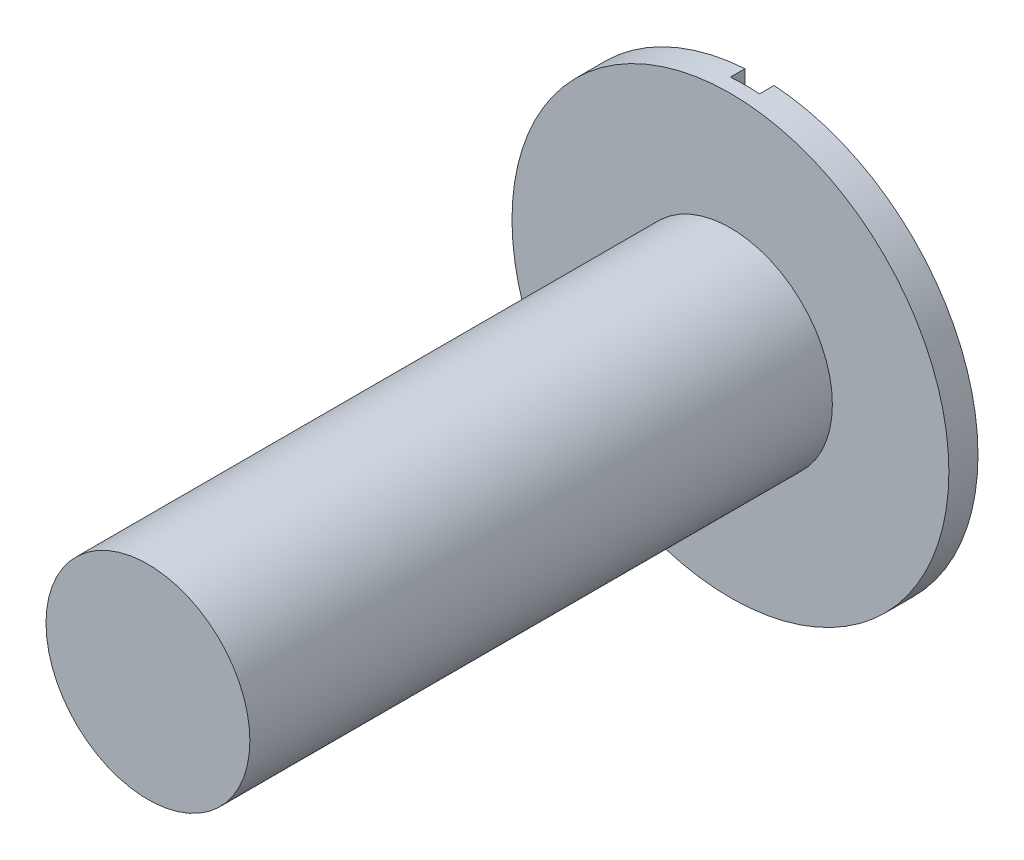
SolidWorks part; units mm, degrees
ref_plane "Alzado" through (0, 0, 0) normal (0, 0, 1) x (1, 0, 0)
ref_plane "Planta" through (0, 0, 0) normal (0, 1, 0) x (1, 0, 0)
ref_plane "Vista lateral" through (0, 0, 0) normal (1, 0, 0) x (0, 0, -1)
sketch "Croquis1" plane through (0, 0, 0) normal (0, 0, 1) x (1, 0, 0)
  circle A0 centre (0, 0) radius 0.75
  dimension "D1" = 1.5
extrude "Saliente-Extruir1" add sketch "Croquis1" along normal blind 0.1
sketch "Croquis2" plane through (0, 0, 0.1) normal (0, 0, 1) x (1, 0, 0)
  circle A0 centre (0, 0) radius 0.35
  dimension "D1" = 0.7
extrude "Saliente-Extruir2" add sketch "Croquis2" along normal blind 2
sketch "Croquis3" plane through (0, 0, 0) normal (0, 0, -1) x (-1, 0, 0)
  line L0 (0, 0.75) -> (0, -0.75) construction
  line L2 (-0.05, 0.8107) -> (0.05, 0.8107)
  line L3 (-0.05, 0.8107) -> (-0.05, -0.8107)
  line L4 (-0.05, -0.8107) -> (0.05, -0.8107)
  line L5 (0.05, 0.8107) -> (0.05, -0.8107)
  line L6 (-0.05, 0.8107) -> (0.05, -0.8107) construction
  line L7 (-0.05, -0.8107) -> (0.05, 0.8107) construction
  circle A0 centre (0, 0) radius 0.75 construction
  point P5 (0, 0)
  dimension "D1" = 0.1
extrude "Cortar-Extruir1" cut sketch "Croquis3" against normal blind 0.05
